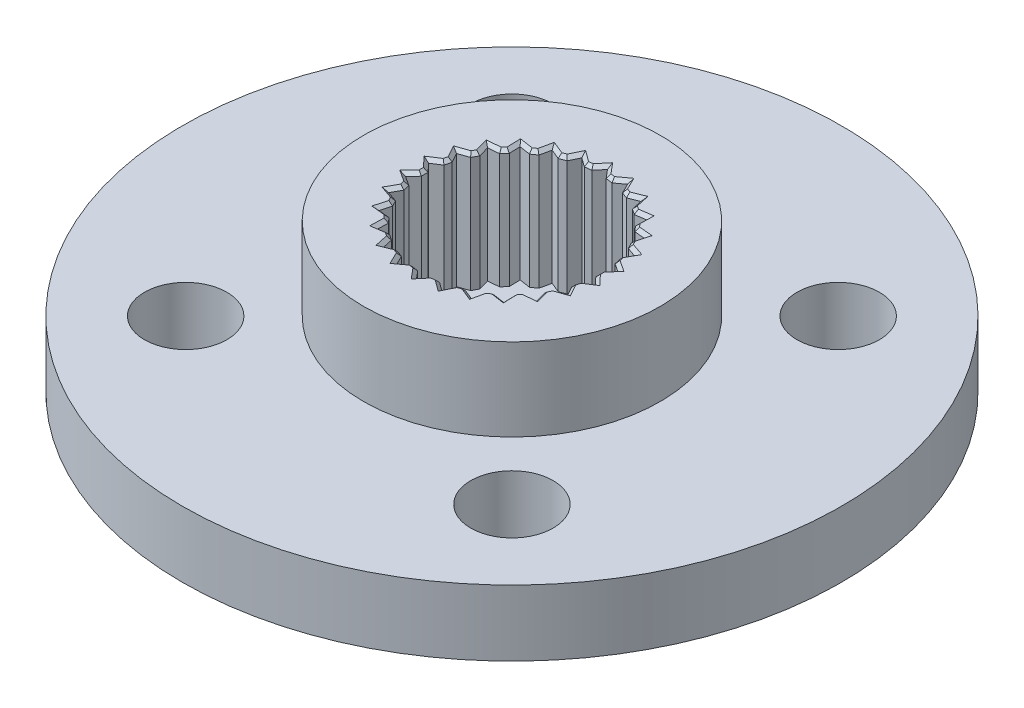
SolidWorks part; units mm, degrees
ref_plane "Front Plane" through (0, 0, 0) normal (0, 0, 1) x (1, 0, 0)
ref_plane "Top Plane" through (0, 0, 0) normal (0, 1, 0) x (1, 0, 0)
ref_plane "Right Plane" through (0, 0, 0) normal (1, 0, 0) x (0, 0, -1)
sketch "Sketch1" plane through (0, 0, 0) normal (0, 1, 0) x (1, 0, 0)
  line L0 (-4.9497, 4.9497) -> (4.9497, 4.9497) construction
  line L1 (4.9497, 4.9497) -> (4.9497, -4.9497) construction
  circle A0 centre (0, 0) radius 10
  circle A1 centre (-4.9497, 4.9497) radius 1.25
  circle A2 centre (4.9497, 4.9497) radius 1.25
  circle A3 centre (4.9497, -4.9497) radius 1.25
  circle A4 centre (-4.9497, -4.9497) radius 1.25
  circle A5 centre (0, 0) radius 7 construction
  circle A6 centre (0, 0) radius 1.5
  dimension "D1" = 20
  dimension "D2" = 2.5
  dimension "D3" = 3
  dimension "D4" = 14
extrude "Boss-Extrude1" add sketch "Sketch1" along normal blind 2
cosmetic thread "Cosmetic Thread1" parameters "D2"=3
cosmetic thread "Cosmetic Thread2" parameters "D2"=3
cosmetic thread "Cosmetic Thread3" parameters "D2"=3
cosmetic thread "Cosmetic Thread4" parameters "D2"=3
sketch "Sketch2" plane through (0, 2, 0) normal (0, 1, 0) x (1, 0, 0)
  circle A0 centre (0, 0) radius 4.5
  circle A1 centre (0, 0) radius 1.5 construction
  circle A2 centre (0, 0) radius 1.5
  dimension "D1" = 9
extrude "Boss-Extrude2" add sketch "Sketch2" along normal blind 2.5
sketch "Sketch3" plane through (0, 4.5, 0) normal (0, 1, 0) x (1, 0, 0)
  circle A0 centre (0, 0) radius 2.25
  dimension "D1" = 4.5
extrude "Cut-Extrude1" cut sketch "Sketch3" against normal blind 3.6
sketch "Sketch7" plane through (0, 4.5, 0) normal (0, 1, 0) x (1, 0, 0)
  line L0 (-1.035, 2.4395) -> (-0.843, 2.5123)
  line L1 (-0.843, 2.5123) -> (-0.7982, 2.6036)
  line L2 (-0.7982, 2.6036) -> (-0.694, 2.8157)
  line L3 (-0.694, 2.8157) -> (-0.5032, 2.6763)
  line L4 (-0.5032, 2.6763) -> (-0.4211, 2.6163)
  line L5 (-0.4211, 2.6163) -> (-0.2173, 2.6411)
  line L6 (-0.2173, 2.6411) -> (-0.1519, 2.719)
  line L7 (-0.1519, 2.719) -> (0, 2.9)
  line L8 (0, 2.9) -> (0.1519, 2.719)
  line L9 (0.1519, 2.719) -> (0.2173, 2.6411)
  line L10 (0.2173, 2.6411) -> (0.4211, 2.6163)
  line L11 (0.4211, 2.6163) -> (0.5032, 2.6763)
  line L12 (0.5032, 2.6763) -> (0.694, 2.8157)
  line L13 (0.694, 2.8157) -> (0.7982, 2.6036)
  line L14 (0.7982, 2.6036) -> (0.843, 2.5123)
  line L15 (0.843, 2.5123) -> (1.035, 2.4395)
  line L16 (1.035, 2.4395) -> (1.1291, 2.4781)
  line L17 (1.1291, 2.4781) -> (1.3477, 2.5678)
  line L18 (1.3477, 2.5678) -> (1.3981, 2.337)
  line L19 (1.3981, 2.337) -> (1.4197, 2.2376)
  line L20 (1.4197, 2.2376) -> (1.5887, 2.1209)
  line L21 (1.5887, 2.1209) -> (1.6893, 2.1359)
  line L22 (1.6893, 2.1359) -> (1.9231, 2.1707)
  line L23 (1.9231, 2.1707) -> (1.9167, 1.9345)
  line L24 (1.9167, 1.9345) -> (1.914, 1.8328)
  line L25 (1.914, 1.8328) -> (2.0501, 1.6791)
  line L26 (2.0501, 1.6791) -> (2.1514, 1.6696)
  line L27 (2.1514, 1.6696) -> (2.3867, 1.6474)
  line L28 (2.3867, 1.6474) -> (2.324, 1.4196)
  line L29 (2.324, 1.4196) -> (2.297, 1.3215)
  line L30 (2.297, 1.3215) -> (2.3924, 1.1397)
  line L31 (2.3924, 1.1397) -> (2.4884, 1.1062)
  line L32 (2.4884, 1.1062) -> (2.7115, 1.0284)
  line L33 (2.7115, 1.0284) -> (2.5962, 0.8221)
  line L34 (2.5962, 0.8221) -> (2.5465, 0.7334)
  line L35 (2.5465, 0.7334) -> (2.5956, 0.534)
  line L36 (2.6809, 0.4785) -> (2.5956, 0.534) construction
  line L37 (2.5956, 0.534) -> (2.6809, 0.4785)
  line L38 (2.6809, 0.4785) -> (2.8789, 0.3496)
  line L39 (2.6809, 0.4785) -> (2.8789, 0.3496)
  line L40 (2.7175, 0.177) -> (2.648, 0.1027)
  line L41 (2.648, 0.1027) -> (2.648, -0.1027)
  line L42 (2.648, -0.1027) -> (2.7175, -0.177)
  line L43 (2.7175, -0.177) -> (2.8789, -0.3496)
  line L44 (2.8789, -0.3496) -> (2.6809, -0.4785)
  line L45 (2.6809, -0.4785) -> (2.5956, -0.534)
  line L46 (2.5956, -0.534) -> (2.5465, -0.7334)
  line L47 (2.5465, -0.7334) -> (2.5962, -0.8221)
  line L48 (2.5962, -0.8221) -> (2.7115, -1.0284)
  line L49 (2.7115, -1.0284) -> (2.4884, -1.1062)
  line L50 (2.4884, -1.1062) -> (2.3924, -1.1397)
  line L51 (2.3924, -1.1397) -> (2.4884, -1.1062) construction
  line L52 (2.3924, -1.1397) -> (2.297, -1.3215)
  line L53 (2.297, -1.3215) -> (2.324, -1.4196)
  line L54 (2.324, -1.4196) -> (2.3867, -1.6474)
  line L55 (2.3867, -1.6474) -> (2.1514, -1.6696)
  line L56 (2.1514, -1.6696) -> (2.0501, -1.6791)
  line L57 (2.0501, -1.6791) -> (1.914, -1.8328)
  line L58 (1.914, -1.8328) -> (1.9167, -1.9345)
  line L59 (1.9167, -1.9345) -> (1.9231, -2.1707)
  line L60 (1.9231, -2.1707) -> (1.6893, -2.1359)
  line L61 (1.6893, -2.1359) -> (1.5887, -2.1209)
  line L62 (1.5887, -2.1209) -> (1.4197, -2.2376)
  line L63 (1.4197, -2.2376) -> (1.3981, -2.337)
  line L64 (1.3981, -2.337) -> (1.3477, -2.5678)
  line L65 (1.3477, -2.5678) -> (1.1291, -2.4781)
  line L66 (1.1291, -2.4781) -> (1.035, -2.4395)
  line L67 (1.035, -2.4395) -> (0.843, -2.5123)
  line L68 (0.843, -2.5123) -> (0.7982, -2.6036)
  line L69 (0.7982, -2.6036) -> (0.694, -2.8157)
  line L70 (0.694, -2.8157) -> (0.5032, -2.6763)
  line L71 (0.5032, -2.6763) -> (0.4211, -2.6163)
  line L72 (0.4211, -2.6163) -> (0.2173, -2.6411)
  line L73 (0.2173, -2.6411) -> (0.1519, -2.719)
  line L74 (0.1519, -2.719) -> (0, -2.9)
  line L75 (0, -2.9) -> (-0.1519, -2.719)
  line L76 (-0.1519, -2.719) -> (-0.2173, -2.6411)
  line L77 (-0.2173, -2.6411) -> (-0.4211, -2.6163)
  line L78 (-0.4211, -2.6163) -> (-0.5032, -2.6763)
  line L79 (-0.5032, -2.6763) -> (-0.694, -2.8157)
  line L80 (-0.694, -2.8157) -> (-0.7982, -2.6036)
  line L81 (-0.7982, -2.6036) -> (-0.843, -2.5123)
  line L82 (-0.843, -2.5123) -> (-1.035, -2.4395)
  line L83 (-1.035, -2.4395) -> (-1.1291, -2.4781)
  line L84 (-1.1291, -2.4781) -> (-1.3477, -2.5678)
  line L85 (-1.3477, -2.5678) -> (-1.3981, -2.337)
  line L86 (-1.3981, -2.337) -> (-1.4197, -2.2376)
  line L87 (-1.4197, -2.2376) -> (-1.5887, -2.1209)
  line L88 (-1.5887, -2.1209) -> (-1.6893, -2.1359)
  line L89 (-1.6893, -2.1359) -> (-1.9231, -2.1707)
  line L90 (-1.9231, -2.1707) -> (-1.9167, -1.9345)
  line L91 (-1.9167, -1.9345) -> (-1.914, -1.8328)
  line L92 (-1.914, -1.8328) -> (-2.0501, -1.6791)
  line L93 (-2.0501, -1.6791) -> (-2.1514, -1.6696)
  line L94 (-2.1514, -1.6696) -> (-2.3867, -1.6474)
  line L95 (-2.3867, -1.6474) -> (-2.324, -1.4196)
  line L96 (-2.324, -1.4196) -> (-2.297, -1.3215)
  line L97 (-2.297, -1.3215) -> (-2.3924, -1.1397)
  line L98 (-2.3924, -1.1397) -> (-2.4884, -1.1062)
  line L99 (-2.4884, -1.1062) -> (-2.7115, -1.0284)
  line L100 (-2.7115, -1.0284) -> (-2.5962, -0.8221)
  line L101 (-2.5962, -0.8221) -> (-2.5465, -0.7334)
  line L102 (-2.5465, -0.7334) -> (-2.5956, -0.534)
  line L103 (-2.5956, -0.534) -> (-2.6809, -0.4785)
  line L104 (-2.6809, -0.4785) -> (-2.8789, -0.3496)
  line L105 (-2.8789, -0.3496) -> (-2.7175, -0.177)
  line L106 (-2.7175, -0.177) -> (-2.648, -0.1027)
  line L107 (-2.648, -0.1027) -> (-2.648, 0.1027)
  line L108 (-2.648, 0.1027) -> (-2.7175, 0.177)
  line L109 (-2.7175, 0.177) -> (-2.8789, 0.3496)
  line L110 (-2.8789, 0.3496) -> (-2.6809, 0.4785)
  line L111 (-2.6809, 0.4785) -> (-2.5956, 0.534)
  line L112 (-2.5956, 0.534) -> (-2.5465, 0.7334)
  line L113 (-2.5465, 0.7334) -> (-2.5962, 0.8221)
  line L114 (-2.5962, 0.8221) -> (-2.7115, 1.0284)
  line L115 (-2.7115, 1.0284) -> (-2.4884, 1.1062)
  line L116 (-2.4884, 1.1062) -> (-2.3924, 1.1397)
  line L117 (-2.3924, 1.1397) -> (-2.297, 1.3215)
  line L118 (-2.297, 1.3215) -> (-2.324, 1.4196)
  line L119 (-2.324, 1.4196) -> (-2.3867, 1.6474)
  line L120 (-2.3867, 1.6474) -> (-2.1514, 1.6696)
  line L121 (-2.1514, 1.6696) -> (-2.0501, 1.6791)
  line L122 (-2.0501, 1.6791) -> (-1.914, 1.8328)
  line L123 (-1.914, 1.8328) -> (-1.9167, 1.9345)
  line L124 (-1.9167, 1.9345) -> (-1.9231, 2.1707)
  line L125 (-1.9231, 2.1707) -> (-1.6893, 2.1359)
  line L126 (-1.6893, 2.1359) -> (-1.5887, 2.1209)
  line L127 (-1.5887, 2.1209) -> (-1.4197, 2.2376)
  line L128 (-1.4197, 2.2376) -> (-1.3981, 2.337)
  line L129 (-1.3981, 2.337) -> (-1.3477, 2.5678)
  line L130 (-1.3477, 2.5678) -> (-1.1291, 2.4781)
  line L131 (-1.1291, 2.4781) -> (-1.035, 2.4395)
  line L132 (-0.843, 2.5123) -> (-0.7982, 2.6036)
  line L133 (-0.694, 2.8157) -> (-0.5032, 2.6763)
  line L134 (-0.4211, 2.6163) -> (-0.2173, 2.6411)
  line L135 (-0.1519, 2.719) -> (0, 2.9)
  line L136 (0.1519, 2.719) -> (0.2173, 2.6411)
  line L137 (0.4211, 2.6163) -> (0.5032, 2.6763)
  line L138 (0.694, 2.8157) -> (0.7982, 2.6036)
  line L139 (1.035, 2.4395) -> (1.3477, 2.5678)
  line L140 (1.3981, 2.337) -> (1.4197, 2.2376)
  line L141 (1.5887, 2.1209) -> (1.6893, 2.1359)
  line L142 (1.9231, 2.1707) -> (1.9167, 1.9345)
  line L143 (1.914, 1.8328) -> (2.0501, 1.6791)
  line L144 (2.1514, 1.6696) -> (2.3867, 1.6474)
  line L145 (2.324, 1.4196) -> (2.297, 1.3215)
  line L146 (2.3924, 1.1397) -> (2.7115, 1.0284)
  line L147 (2.5962, 0.8221) -> (2.5465, 0.7334)
  line L148 (2.8789, 0.3496) -> (2.7175, 0.177)
extrude "Cut-Extrude2" cut sketch "Sketch7" against normal up to surface (3.6 mm away) contours L148 L38 L37 L35 L34 L33 L32 L31 L30 L29 L28 L27 L26 L25 L24 L23 L22 L21 L20 L19 L18 L17 L16 L15 L14 L13 L12 L11 L10 L9 L8 L7 L6 L5 L4 L3 L2 L1 L0 L131 L130 L129 L128 L127 L126 L125 L124 L123 L122 L121 L120 up to face at (0, 0.9, 1.5)
chamfer "Chamfer1" distance 0.1 angle 45 78 edges at (-2.629, 4.5, -0.8809) (-2.5711, 4.5, -0.6337) (-2.7372, 4.5, -0.4418) (-2.7634, 4.5, -0.2261) (-2.648, 4.5, 0) (-2.7634, 4.5, 0.2261) (-2.7372, 4.5, 0.4418) (-2.5711, 4.5, 0.6337) (-2.629, 4.5, 0.8809) (-2.552, 4.5, 1.084) (-2.3447, 4.5, 1.2306) (-2.3418, 4.5, 1.4844) (-2.2184, 4.5, 1.6632) (-1.9821, 4.5, 1.756) (-1.9185, 4.5, 2.0017) (-1.7559, 4.5, 2.1458) (-1.5042, 4.5, 2.1793) (-1.3837, 4.5, 2.4027) (-1.1913, 4.5, 2.5037) (-0.939, 4.5, 2.4759) (-0.7685, 4.5, 2.664) (-0.5576, 4.5, 2.716) (-0.3192, 4.5, 2.6287) (-0.1086, 4.5, 2.7705) (0.1086, 4.5, 2.7705) (0.3192, 4.5, 2.6287) (0.5576, 4.5, 2.716) (0.7685, 4.5, 2.664) (0.939, 4.5, 2.4759) (1.1913, 4.5, 2.5037) (1.3837, 4.5, 2.4027) (1.5042, 4.5, 2.1793) (1.7559, 4.5, 2.1458) (1.9185, 4.5, 2.0017) (1.9821, 4.5, 1.756) (2.2184, 4.5, 1.6632) (2.3418, 4.5, 1.4844) (2.3447, 4.5, 1.2306) (2.552, 4.5, 1.084) (2.629, 4.5, 0.8809) (2.5711, 4.5, 0.6337) (2.7372, 4.5, 0.4418) (2.7634, 4.5, 0.2261) (2.648, 4.5, 0) (2.7634, 4.5, -0.2261) (2.7372, 4.5, -0.4418) (2.5711, 4.5, -0.6337) (2.629, 4.5, -0.8809) (2.552, 4.5, -1.084) (2.3447, 4.5, -1.2306) (2.3418, 4.5, -1.4844) (2.2184, 4.5, -1.6632) (1.9821, 4.5, -1.756) (1.9185, 4.5, -2.0017) (1.7559, 4.5, -2.1458) (1.5042, 4.5, -2.1793) (1.3837, 4.5, -2.4027) (1.1913, 4.5, -2.5037) (0.939, 4.5, -2.4759) (0.7685, 4.5, -2.664) (0.5576, 4.5, -2.716) (0.3192, 4.5, -2.6287) (0.1086, 4.5, -2.7705) (-0.1086, 4.5, -2.7705) (-0.3192, 4.5, -2.6287) (-0.5576, 4.5, -2.716) (-0.7685, 4.5, -2.664) (-0.939, 4.5, -2.4759) (-1.1913, 4.5, -2.5037) (-1.3837, 4.5, -2.4027) (-1.5042, 4.5, -2.1793) (-1.7559, 4.5, -2.1458) (-1.9185, 4.5, -2.0017) (-1.9821, 4.5, -1.756) (-2.2184, 4.5, -1.6632) (-2.3418, 4.5, -1.4844) (-2.3447, 4.5, -1.2306) (-2.552, 4.5, -1.084)
